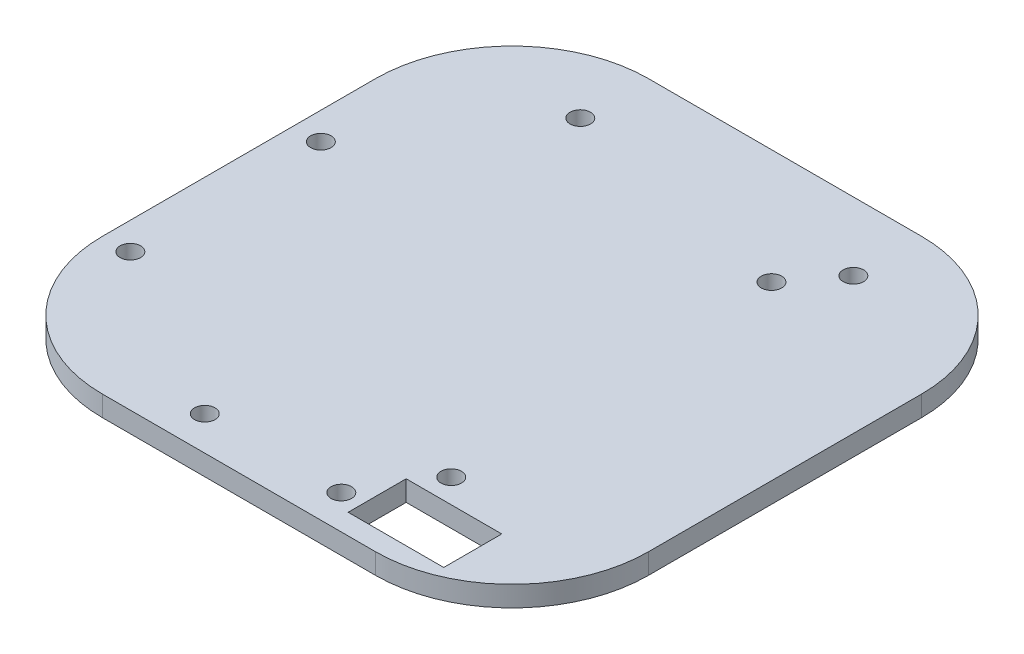
SolidWorks part; units mm, degrees
material "Pine"
ref_plane "Front Plane" through (0, 0, 0) normal (0, 0, 1) x (1, 0, 0)
ref_plane "Top Plane" through (0, 0, 0) normal (0, 1, 0) x (1, 0, 0)
ref_plane "Right Plane" through (0, 0, 0) normal (1, 0, 0) x (0, 0, -1)
sketch "Sketch3" plane through (0, 0, 0) normal (0, 1, 0) x (1, 0, 0)
  line L1 (0, 0) -> (80, 0)
  line L2 (0, 0) -> (0, 80)
  line L3 (0, 80) -> (80, 80)
  line L4 (80, 0) -> (80, 80)
  dimension "D1" = 80
  dimension "D2" = 80
extrude "Boss-Extrude1" add sketch "Sketch3" along normal blind 3
fillet "Fillet3" radius 20 1 edges at (0, 1.5, -80)
fillet "Fillet4" radius 20 1 edges at (80, 1.5, -80)
fillet "Fillet5" radius 20 1 edges at (80, 1.5, 0)
fillet "Fillet6" radius 20 1 edges at (0, 1.5, 0)
sketch "Sketch12" plane through (0, 3, 0) normal (0, 1, 0) x (1, 0, 0)
  line L0 (20, 0) -> (60, 0) construction
  line L1 (0, 60) -> (0, 20) construction
  line L2 (80, 20) -> (80, 60) construction
  circle A0 centre (30, 5) radius 1.5
  circle A1 centre (50, 5) radius 1.5
  dimension "D1" = 5
  dimension "D3" = 5
  dimension "D2" = 30
  dimension "D4" = 30
extrude "Cut-Extrude6" cut sketch "Sketch12" against normal blind 3
sketch "Sketch13" plane through (0, 3, 0) normal (0, 1, 0) x (1, 0, 0)
  line L0 (0, 60) -> (0, 20) construction
  line L1 (60, 80) -> (20, 80) construction
  line L2 (80, 20) -> (80, 60) construction
  circle A0 centre (20, 70) radius 1.5
  circle A1 centre (60, 70) radius 1.5
  dimension "D1" = 20
  dimension "D3" = 20
  dimension "D2" = 10
  dimension "D4" = 10
extrude "Cut-Extrude7" cut sketch "Sketch13" against normal blind 3
sketch "Sketch14" plane through (0, 3, 0) normal (0, 1, 0) x (1, 0, 0)
  line L0 (0, 60) -> (0, 20) construction
  line L2 (60, 80) -> (20, 80) construction
  circle A0 centre (4, 20.1) radius 1.5
  circle A1 centre (4, 48) radius 1.5
  circle A2 centre (54.8, 63.2) radius 1.5
  circle A3 centre (56.1, 15) radius 1.5
  dimension "D1" = 4
  dimension "D3" = 4
  dimension "D5" = 50.8
  dimension "D7" = 1.3
  dimension "D2" = 32
  dimension "D4" = 27.9
  dimension "D6" = 15.2
  dimension "D8" = 5.1
extrude "Cut-Extrude8" cut sketch "Sketch14" against normal blind 10
sketch "Sketch15" plane through (0, 3, 0) normal (0, 1, 0) x (1, 0, 0)
  line L0 (20, 0) -> (60, 0) construction
  line L1 (53, 11.5) -> (67, 11.5)
  line L2 (53, 11.5) -> (53, 3)
  line L3 (53, 3) -> (67, 3)
  line L4 (67, 11.5) -> (67, 3)
  line L5 (0, 60) -> (0, 20) construction
  dimension "D1" = 14
  dimension "D2" = 8.5
  dimension "D3" = 3
  dimension "D4" = 53
extrude "Cut-Extrude9" cut sketch "Sketch15" against normal blind 10
